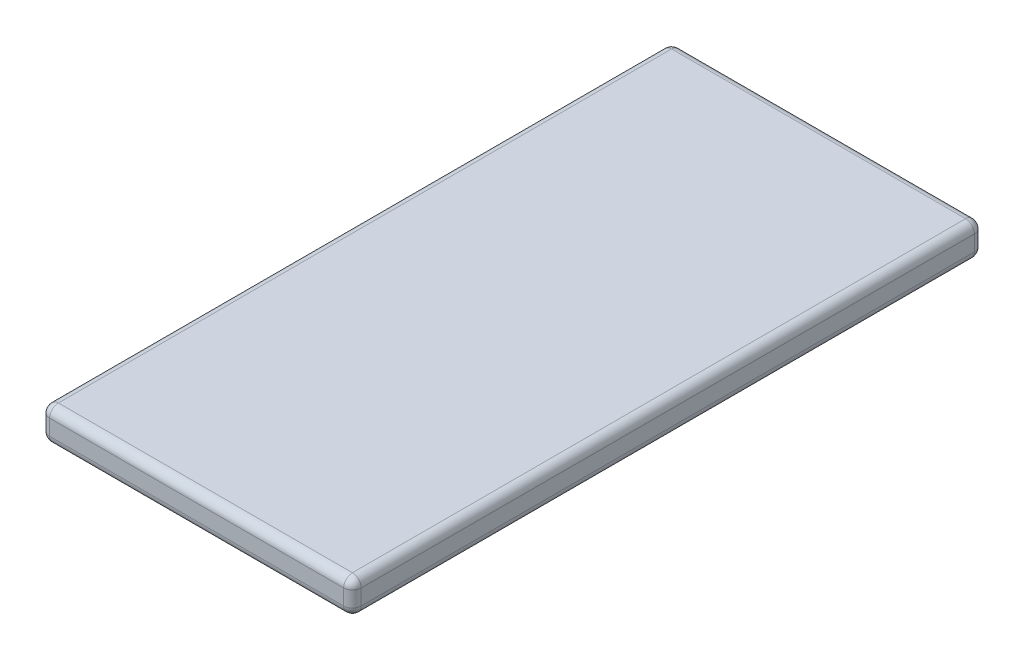
SolidWorks part; units mm, degrees
ref_plane "正面" through (0, 0, 0) normal (0, 0, 1) x (1, 0, 0)
ref_plane "平面" through (0, 0, 0) normal (0, 1, 0) x (1, 0, 0)
ref_plane "右側面" through (0, 0, 0) normal (1, 0, 0) x (0, 0, -1)
sketch "ｽｹｯﾁ1" plane through (0, 0, 0) normal (0, 1, 0) x (1, 0, 0)
  line L1 (-35.47, -71.795) -> (35.47, -71.795)
  line L2 (-35.47, -71.795) -> (-35.47, 71.795)
  line L3 (-35.47, 71.795) -> (35.47, 71.795)
  line L4 (35.47, -71.795) -> (35.47, 71.795)
  line L5 (-35.47, -71.795) -> (35.47, 71.795) construction
  line L6 (-35.47, 71.795) -> (35.47, -71.795) construction
  point P0 (0, 0)
  dimension "D1" = 143.59
  dimension "D2" = 70.94
extrude "ﾎﾞｽ - 押し出し1" add sketch "ｽｹｯﾁ1" along normal blind 7.56
ref_plane "平面1" through (-35.47, 7.56, -71.795) normal (0, 0, 1) x (1, 0, 0)
fillet "ﾌｨﾚｯﾄ1" radius 2 12 edges at (35.47, 3.78, 71.795) (35.47, 3.78, -71.795) (-35.47, 3.78, -71.795) (-35.47, 3.78, 71.795) (0, 7.56, 71.795) (-35.47, 7.56, 0) (0, 7.56, -71.795) (35.47, 7.56, 0) (0, 0, -71.795) (-35.47, 0, 0) (0, 0, 71.795) (35.47, 0, 0)
